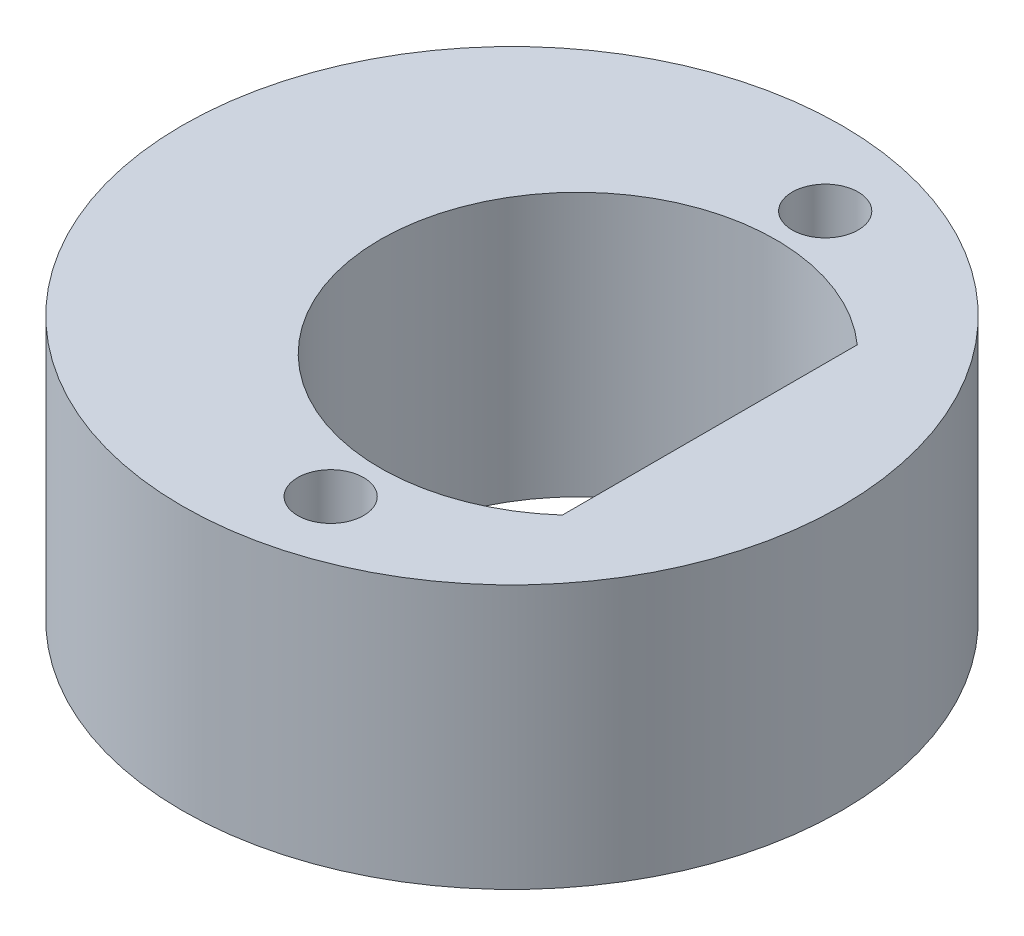
SolidWorks part; units mm, degrees
ref_plane "Front Plane" through (0, 0, 0) normal (0, 0, 1) x (1, 0, 0)
ref_plane "Top Plane" through (0, 0, 0) normal (0, 1, 0) x (1, 0, 0)
ref_plane "Right Plane" through (0, 0, 0) normal (1, 0, 0) x (0, 0, -1)
sketch "Sketch1" plane through (0, 0, 0) normal (0, 1, 0) x (1, 0, 0)
  line L0 (-1, 0) -> (0, 0) construction
  circle A0 centre (0, 0) radius 3
  circle A1 centre (-1, 0) radius 5
  dimension "D1" = 6
  dimension "D2" = 10
  dimension "D3" = 1
extrude "Boss-Extrude1" add sketch "Sketch1" along normal blind 4
sketch "Sketch2" plane through (0, 4, 0) normal (0, 1, 0) x (1, 0, 0)
  line L0 (0, 3.75) -> (0, -3.75) construction
  circle A0 centre (0, 3.75) radius 0.5
  circle A1 centre (0, -3.75) radius 0.5
  point P4 (0, 0)
  dimension "D1" = 1
  dimension "D2" = 1
  dimension "D3" = 0
  dimension "D4" = 7.5
extrude "Cut-Extrude1" cut sketch "Sketch2" against normal through all
sketch "Sketch3" plane through (0, 0, 0) normal (0, -1, 0) x (1, 0, 0)
  line L0 (2, 2.2361) -> (2, -2.2361)
  line L1 (0, 0) -> (3, 0) construction
  circle A0 centre (0, 0) radius 3
  circle M7 centre (0, 0) radius 3
  dimension "D2" = 6
  dimension "D1" = 2
extrude "Boss-Extrude2" add sketch "Sketch3" against normal blind 4 contours L1 L0 M7 | L0 L1 M7
